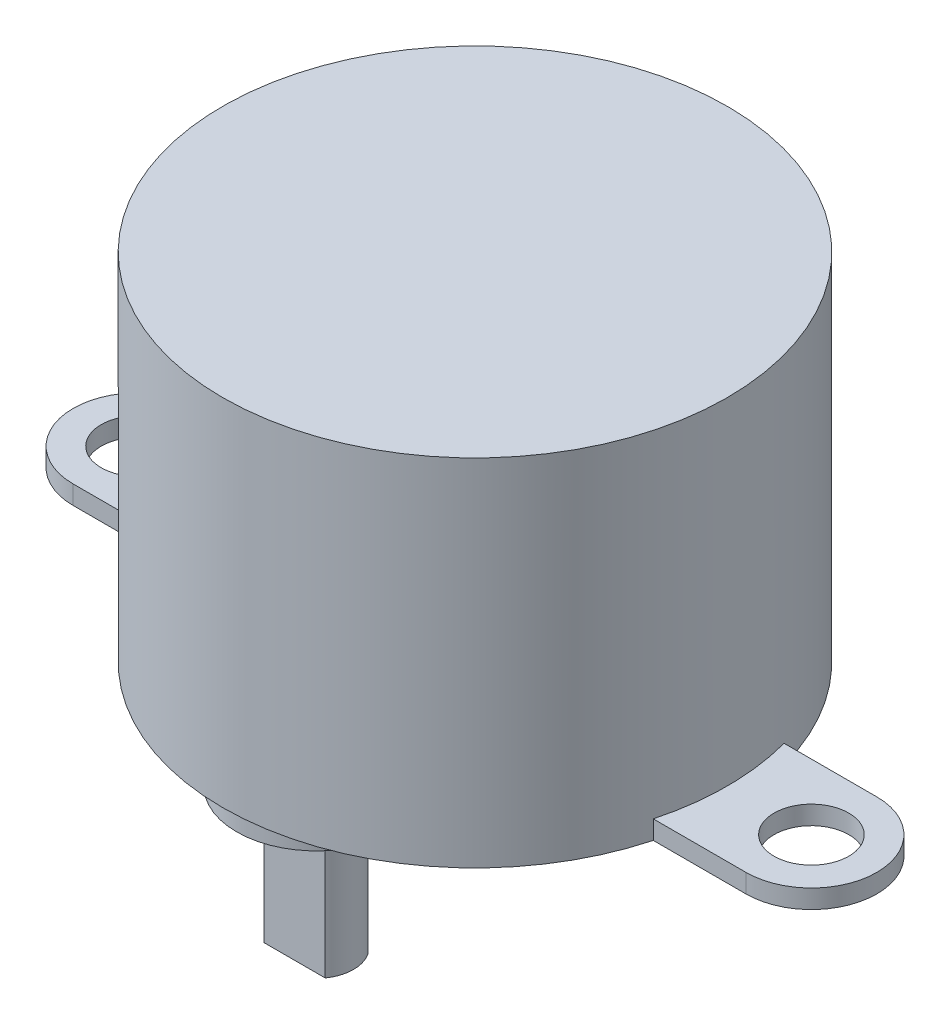
SolidWorks part; units mm, degrees
ref_plane "Front Plane" through (0, 0, 0) normal (0, 0, 1) x (1, 0, 0)
ref_plane "Top Plane" through (0, 0, 0) normal (0, 1, 0) x (1, 0, 0)
ref_plane "Right Plane" through (0, 0, 0) normal (1, 0, 0) x (0, 0, -1)
sketch "Sketch1" plane through (0, 0, 0) normal (0, 1, 0) x (1, 0, 0)
  circle A0 centre (0, 0) radius 13.5
  dimension "D1" = 27
extrude "Boss-Extrude1" add sketch "Sketch1" along normal blind 19
sketch "Sketch2" plane through (0, 0, 0) normal (0, -1, 0) x (1, 0, 0)
  line L0 (-20.63, 0) -> (23.9701, 0) construction
  line L1 (0, 16.5601) -> (0, -15.9146) construction
  line L2 (18, 3.5) -> (13.0384, 3.5)
  line L3 (18, -3.5) -> (13.0384, -3.5)
  arc A0 (18, -3.5) -> (18, 3.5) centre (18, 0) ccw
  circle A1 centre (0, 0) radius 13.5 construction
  arc A2 (13.0384, -3.5) -> (13.0384, 3.5) centre (0, 0) ccw
  circle A3 centre (18, 0) radius 2
  dimension "D1" = 8
  dimension "D3" = 4
  dimension "D2" = 7
extrude "Boss-Extrude2" add sketch "Sketch2" against normal blind 1
mirror "Mirror1" about plane through (0, 0, 0) normal (1, 0, 0) of "Boss-Extrude2"
sketch "Sketch4" plane through (0, 0, 0) normal (0, -1, 0) x (1, 0, 0)
  line L0 (0, 15.0256) -> (0, -15.6301) construction
  line L1 (-17.8926, 8.5) -> (22.7629, 8.5) construction
  circle A0 centre (0, 8.5) radius 4.25
  dimension "D2" = 8.5
  dimension "D1" = 8.5
extrude "Boss-Extrude3" add sketch "Sketch4" along normal blind 1.5 contours A0
sketch "Sketch5" plane through (0, -1.5, 0) normal (0, -1, 0) x (1, 0, 0)
  circle A0 centre (0, 8.5) radius 2
  circle A1 centre (0, 8.5) radius 4.25 construction
  dimension "D1" = 4
extrude "Boss-Extrude4" add sketch "Sketch5" along normal blind 1.5
sketch "Sketch6" plane through (0, -3, 0) normal (0, -1, 0) x (1, 0, 0)
  line L0 (-1.6363, 9.65) -> (1.6363, 9.65)
  line L1 (-1.6363, 7.35) -> (1.6363, 7.35)
  line L2 (-6.6205, 8.5) -> (7.5992, 8.5) construction
  arc A0 (1.6363, 7.35) -> (1.6363, 9.65) centre (0, 8.5) ccw
  circle A1 centre (0, 8.5) radius 2
  arc A2 (-1.6363, 9.65) -> (-1.6363, 7.35) centre (0, 8.5) ccw
  dimension "D2" = 2.3
  dimension "D1" = 0
extrude "Boss-Extrude5" add sketch "Sketch6" along normal blind 6
